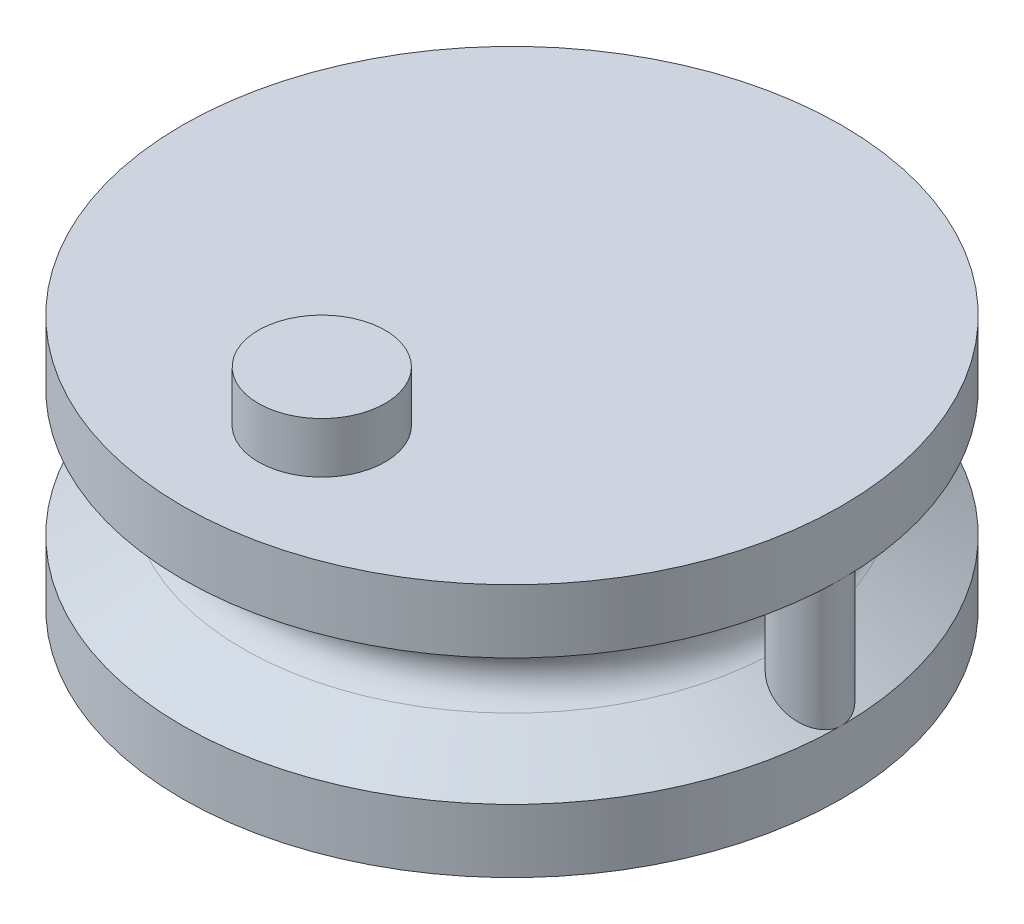
SolidWorks part; units mm, degrees
ref_plane "Front Plane" through (0, 0, 0) normal (0, 0, 1) x (1, 0, 0)
ref_plane "Top Plane" through (0, 0, 0) normal (0, 1, 0) x (1, 0, 0)
ref_plane "Right Plane" through (0, 0, 0) normal (1, 0, 0) x (0, 0, -1)
sketch "Sketch1" plane through (0, 0, 0) normal (0, 1, 0) x (1, 0, 0)
  circle A0 centre (0, 0) radius 10
  dimension "2" = 20
extrude "Boss-Extrude1" add sketch "Sketch1" along normal blind 10
ref_axis "Axis1" through (0, 10, 0) along (0, -1, 0)
sketch "Sketch2" plane through (0, 0, 0) normal (1, 0, 0) x (0, 0, -1)
  line L0 (10, 0) -> (10, 10) construction
  line L1 (10, 10) -> (13, 10)
  line L2 (13, 10) -> (13, 7.5)
  line L3 (13, 7.5) -> (10.6094, 6.0734)
  line L4 (10, 0) -> (13, 0)
  line L5 (13, 0) -> (13, 2.5)
  line L6 (13, 2.5) -> (10.6094, 3.9266)
  line L7 (11.25, 10) -> (11.25, 0) construction
  line L8 (10, 10) -> (9.25, 10)
  line L9 (10, 10) -> (-10, 10) construction
  line L10 (9.25, 10) -> (9.25, 0)
  line L11 (-10, 0) -> (10, 0) construction
  line L12 (9.25, 0) -> (10, 0)
  arc A0 (10.6094, 6.0734) -> (10.6094, 3.9266) centre (11.25, 5) ccw
  dimension "D1" = 2.5
  dimension "D2" = 2.5
  dimension "D3" = 3
  dimension "D4" = 2
revolve "Revolve1" add sketch "Sketch2" angle 360 about axis through (0, 10, 0) along (0, -1, 0)
sketch "Sketch3" plane through (0, 0, 0) normal (0, -1, 0) x (1, 0, 0)
  circle A0 centre (0, 0) radius 5
  dimension "D1" = 10
extrude "Cut-Extrude1" cut sketch "Sketch3" against normal blind 5
sketch "Sketch4" plane through (0, 10, 0) normal (0, 1, 0) x (1, 0, 0)
  line L0 (0, 0) -> (0, -7.5) construction
  circle A0 centre (0, -7.5) radius 2.5
  dimension "D1" = 7.5
  dimension "D2" = 5
extrude "Boss-Extrude2" add sketch "Sketch4" along normal blind 2
sketch "Sketch5" plane through (0, 10, 0) normal (0, 1, 0) x (1, 0, 0)
  line L0 (0, 0) -> (11.75, 0) construction
  circle A0 centre (11.75, 0) radius 1.25
  circle A1 centre (0, 0) radius 13 construction
  dimension "D1" = 2.5
extrude "Boss-Extrude3" add sketch "Sketch5" against normal up to surface (10 mm away) up to face at (0, 0, -5)
